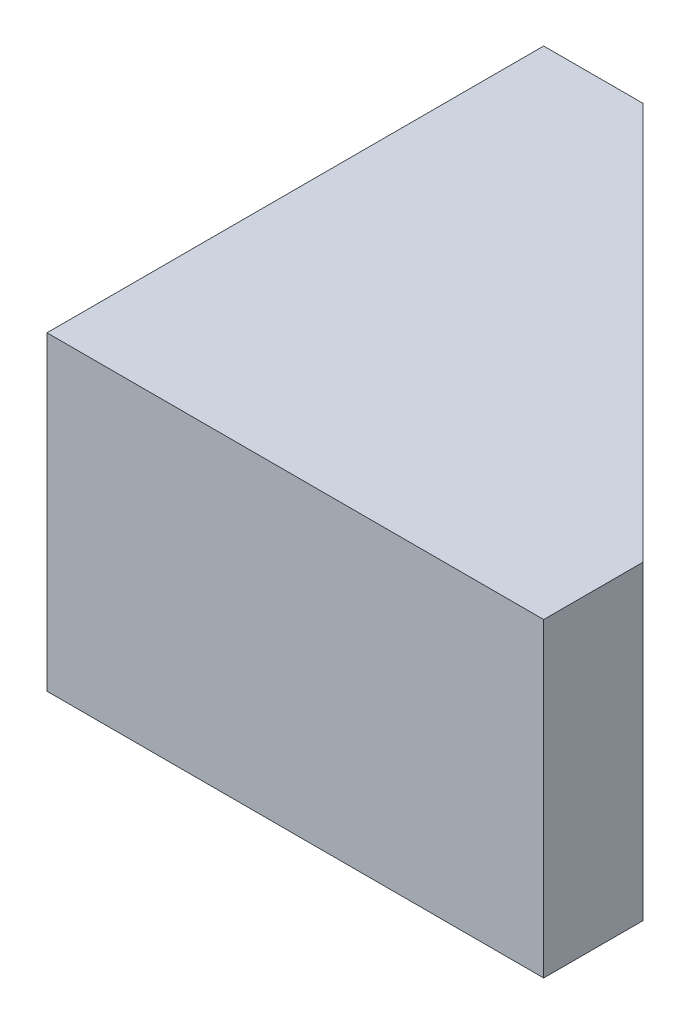
SolidWorks part; units mm, degrees
ref_plane "Alzado" through (0, 0, 0) normal (0, 0, 1) x (1, 0, 0)
ref_plane "Planta" through (0, 0, 0) normal (0, 1, 0) x (1, 0, 0)
ref_plane "Vista lateral" through (0, 0, 0) normal (1, 0, 0) x (0, 0, -1)
sketch "Croquis1" plane through (0, 0, 0) normal (0, 1, 0) x (1, 0, 0)
  line L0 (0, 0) -> (-40, 0)
  line L1 (-40, 0) -> (-40, 40)
  line L2 (-40, 40) -> (-32, 40)
  line L3 (-32, 40) -> (0, 8)
  line L4 (0, 8) -> (0, 0)
  dimension "D1" = 40
  dimension "D2" = 40
  dimension "D3" = 8
  dimension "D4" = 8
extrude "Saliente-Extruir1" add sketch "Croquis1" along normal blind 25
